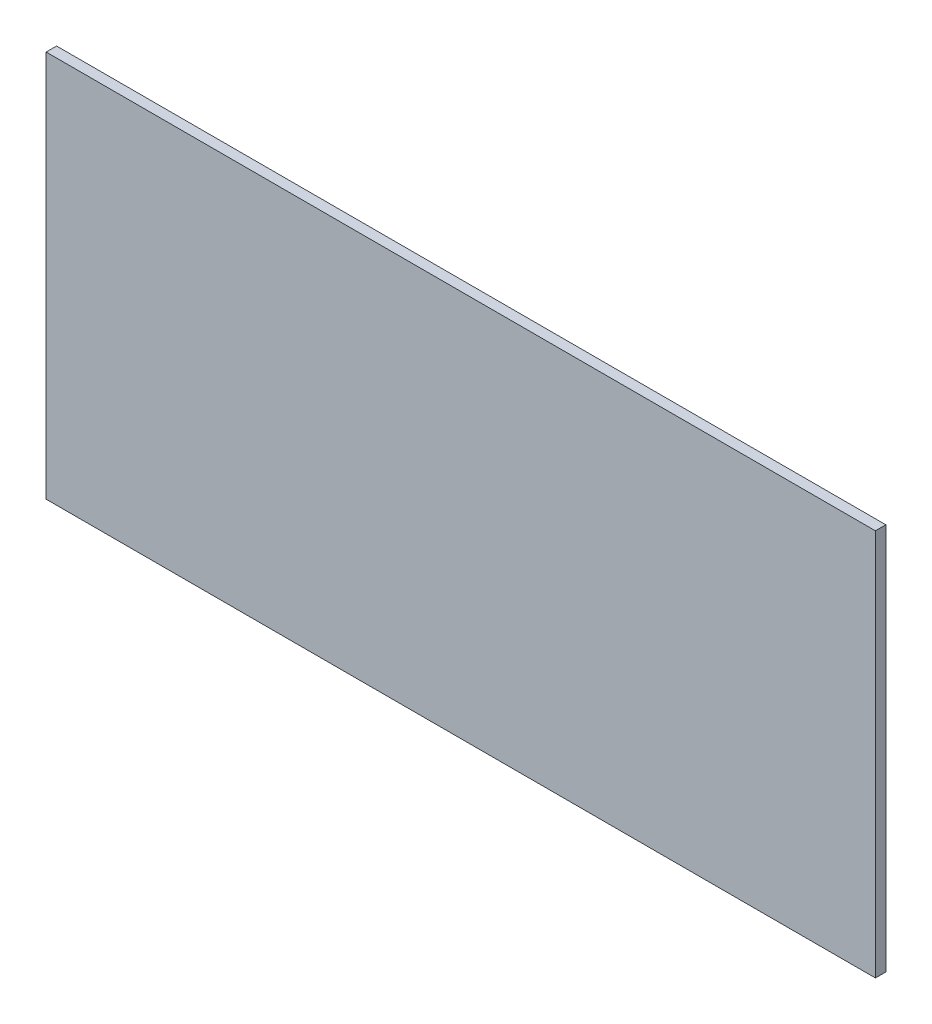
SolidWorks part; units mm, degrees
material "Pine"
ref_plane "Front Plane" through (0, 0, 0) normal (0, 0, 1) x (1, 0, 0)
ref_plane "Top Plane" through (0, 0, 0) normal (0, 1, 0) x (1, 0, 0)
ref_plane "Right Plane" through (0, 0, 0) normal (1, 0, 0) x (0, 0, -1)
sketch "Sketch1" plane through (0, 0, 0) normal (0, 0, 1) x (1, 0, 0)
  line L1 (-473.3294, 454.025) -> (473.3294, 454.025)
  line L2 (-473.3294, 454.025) -> (-473.3294, 11.9063)
  line L3 (-473.3294, 11.9063) -> (473.3294, 11.9063)
  line L4 (473.3294, 454.025) -> (473.3294, 11.9063)
  line L6 (473.3294, 454.025) -> (473.3294, 11.9062) construction
  line L7 (-480.2035, 11.9063) -> (480.2035, 11.9063) construction
extrude "Boss-Extrude1" add sketch "Sketch1" against normal up to surface (11.9063 mm away)
